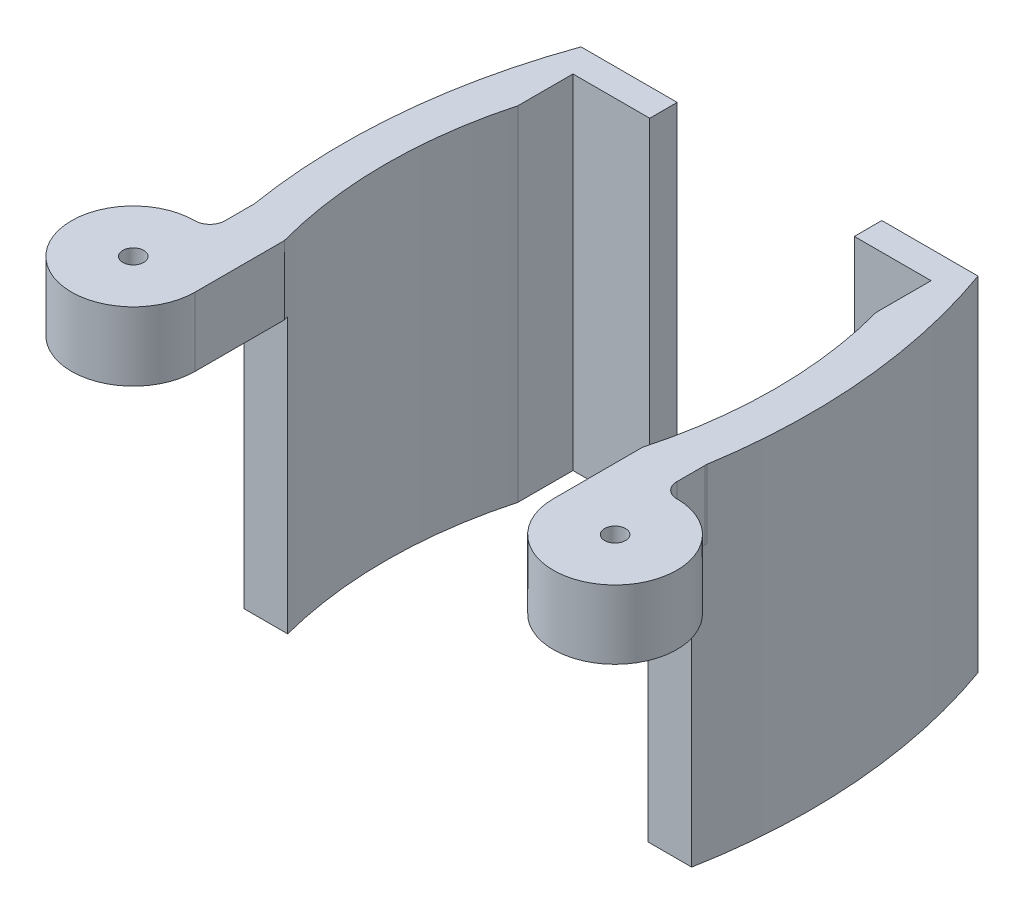
SolidWorks part; units mm, degrees
ref_plane "Front Plane" through (0, 0, 0) normal (0, 0, 1) x (1, 0, 0)
ref_plane "Top Plane" through (0, 0, 0) normal (0, 1, 0) x (1, 0, 0)
ref_plane "Right Plane" through (0, 0, 0) normal (1, 0, 0) x (0, 0, -1)
sketch "Sketch1" plane through (0, 0, 0) normal (0, 1, 0) x (1, 0, 0)
  line L0 (-9.8555, -63.7645) -> (-9.8555, -55.7645)
  line L1 (-9.8555, -21.7645) -> (-9.8555, -13.7645)
  line L2 (-9.8555, -13.7645) -> (-21.0253, -13.7645)
  line L3 (-21.0253, -13.7645) -> (-21.0253, -9.7645)
  line L4 (-21.0253, -9.7645) -> (-7.0253, -9.7645)
  line L5 (-35.9177, -13.7645) -> (-35.9177, -65.301) construction
  line L6 (-50.8101, -9.7645) -> (-64.8101, -9.7645)
  line L7 (-50.8101, -13.7645) -> (-50.8101, -9.7645)
  line L8 (-61.9799, -13.7645) -> (-50.8101, -13.7645)
  line L9 (-61.9799, -21.7645) -> (-61.9799, -13.7645)
  line L10 (-61.9799, -63.7645) -> (-61.9799, -55.7645)
  arc A0 (-9.8555, -63.7645) -> (-3.3512, -55.1175) centre (-0.8555, -63.7645) ccw
  arc A1 (-9.8555, -55.7645) -> (-9.8555, -21.7645) centre (-72.1785, -38.7645) ccw
  arc A2 (-7.0253, -9.7645) -> (-3.3512, -55.1175) centre (-89.1976, -39.2467) cw
  arc A3 (-64.8101, -9.7645) -> (-68.4842, -55.1175) centre (17.3623, -39.2467) ccw
  arc A4 (-61.9799, -55.7645) -> (-61.9799, -21.7645) centre (0.3432, -38.7645) cw
  arc A5 (-61.9799, -63.7645) -> (-68.4842, -55.1175) centre (-70.9799, -63.7645) cw
  dimension "D4" = 64.6
  dimension "D5" = 9
  dimension "D1" = 8
  dimension "D2" = 8
  dimension "D3" = 4
  dimension "D6" = 50
  dimension "D7" = 14
  dimension "D8" = 4.9
  dimension "D9" = 11.1698
extrude "Boss-Extrude1" add sketch "Sketch1" against normal blind 50
sketch "Sketch2" plane through (0, -50, 0) normal (0, -1, 0) x (1, 0, 0)
  circle A0 centre (-70.9799, 63.7645) radius 9
  circle A1 centre (-0.8555, 63.7645) radius 9
extrude "Cut-Extrude1" cut sketch "Sketch2" against normal blind 40
sketch "Sketch3" plane through (0, -50, 0) normal (0, -1, 0) x (1, 0, 0)
  line L0 (-68.4842, 55.1175) -> (-62.1528, 55.1175)
  line L1 (-62.1528, 55.1175) -> (-3.3512, 55.1175)
  line L2 (-3.3512, 55.1175) -> (-3.3512, 65.1021)
  line L3 (-3.3512, 65.1021) -> (-68.4842, 65.1021)
  line L4 (-68.4842, 65.1021) -> (-68.4842, 55.1175)
  arc A0 (-61.9799, 55.7645) -> (-61.9799, 21.7645) centre (0.3432, 38.7645) ccw construction
extrude "Cut-Extrude2" cut sketch "Sketch3" against normal blind 40
sketch "Sketch4" plane through (0, 0, 0) normal (0, 1, 0) x (1, 0, 0)
  line L0 (-68.8006, -53.2984) -> (-66.6672, -54.3894)
  line L1 (-66.6672, -54.3894) -> (-69.1301, -56.5741)
  line L2 (-69.1301, -56.5741) -> (-70.1938, -54.7989)
  line L3 (-3.0222, -53.2343) -> (-4.8299, -54.3174)
  line L4 (-4.8299, -54.3174) -> (-2.8281, -56.5741)
  line L5 (-2.8281, -56.5741) -> (-1.5175, -54.7889)
  arc A0 (-70.1938, -54.7989) -> (-68.8006, -53.2984) centre (-70.0805, -53.5071) ccw
  arc A1 (-68.4842, -55.1175) -> (-61.9799, -63.7645) centre (-70.9799, -63.7645) ccw construction
  arc A2 (-3.0222, -53.2343) -> (-1.5175, -54.7889) centre (-1.6211, -53.3837) ccw
  arc A3 (-9.8555, -63.7645) -> (-3.3512, -55.1175) centre (-0.8555, -63.7645) ccw construction
  arc A4 (-64.8101, -9.7645) -> (-68.4842, -55.1175) centre (17.3623, -39.2467) ccw construction
  arc A5 (-3.3512, -55.1175) -> (-7.0253, -9.7645) centre (-89.1976, -39.2467) ccw construction
extrude "Boss-Extrude2" add sketch "Sketch4" against normal blind 10
sketch "Sketch5" plane through (0, 0, 0) normal (0, 1, 0) x (1, 0, 0)
  circle A0 centre (-70.9799, -63.7645) radius 1.525
  circle A1 centre (-0.8555, -63.7645) radius 1.525
  dimension "D1" = 3.05
  dimension "D2" = 3.05
extrude "Cut-Extrude3" cut sketch "Sketch5" against normal blind 10
sketch "Sketch7" plane through (0, 0, 0) normal (0, 1, 0) x (1, 0, 0)
  line L0 (-9.8555, -63.7645) -> (-9.8555, -68.7645)
  line L1 (8.1445, -63.7645) -> (8.1445, -68.7645)
  line L2 (-61.9799, -63.7645) -> (-61.9799, -68.7645)
  line L3 (-79.9799, -63.7645) -> (-79.9799, -68.7645)
  circle A0 centre (-70.9799, -68.7645) radius 9
  circle A2 centre (-70.9799, -63.7645) radius 9
  circle A3 centre (-0.8555, -63.7645) radius 9
  circle A4 centre (-0.8555, -68.7645) radius 9
  arc M3 (-9.8555, -63.7645) -> (-1.5175, -54.7889) centre (-0.8555, -63.7645) ccw
  dimension "D3" = 18
  dimension "D4" = 18
  dimension "D1" = 5
  dimension "D2" = 5
extrude "Boss-Extrude3" add sketch "Sketch7" against normal up to surface (10 mm away) contours A4 A3 | A4 L1 M3 | A4 L0 M3 | A2 A0 L2 | A2 A0 | A2 L3 A0
sketch "Sketch8" plane through (0, 0, 0) normal (0, 1, 0) x (1, 0, 0)
  circle A0 centre (-70.9799, -63.7645) radius 1.525
  circle A1 centre (-0.8555, -63.7645) radius 1.525
extrude "Boss-Extrude4" add sketch "Sketch8" against normal up to surface (10 mm away) up to face at (-0.8555, -10, 65.2895)
sketch "Sketch9" plane through (0, 0, 0) normal (0, 1, 0) x (1, 0, 0)
  line L0 (-68.8006, -53.2984) -> (-68.8006, -60.0453)
  line L1 (-3.0246, -53.2357) -> (-3.0246, -60.0298)
  line L2 (-79.9799, -53.2984) -> (-79.9799, -68.7645)
  line L3 (-68.8006, -53.2984) -> (-79.9799, -53.2984)
  line L4 (8.1445, -68.7645) -> (8.1445, -53.2357)
  line L5 (8.1445, -53.2357) -> (-3.0246, -53.2357)
  circle A0 centre (-70.9698, -68.7687) radius 8.9891
  circle A1 centre (-0.8555, -68.7645) radius 9
  arc A2 (-70.9698, -59.7796) -> (-68.8006, -57.6104) centre (-70.9698, -57.6104) ccw
  arc A3 (-0.8555, -59.7645) -> (-3.0246, -57.5955) centre (-0.8555, -57.5955) cw
  arc A4 (-70.9698, -59.7796) -> (-79.9799, -68.7645) centre (-70.9949, -68.7645) ccw
  line M5 (8.1445, -68.7645) -> (8.1445, -63.7645)
  arc M6 (8.1445, -63.7645) -> (-1.5175, -54.7889) centre (-0.8555, -63.7645) ccw
  arc M7 (-1.5175, -54.7889) -> (-3.0222, -53.2343) centre (-1.6211, -53.3837) cw
  dimension "D1" = 2.1692
  dimension "D2" = 90
  dimension "D3" = 12.7244
extrude "Cut-Extrude5" cut sketch "Sketch9" against normal blind 10 contours A4 A2 L0 L3 L2 | A3 A1 L1 M5 M6 M7 | L4 L5 L1 M7 M6
sketch "Sketch10" plane through (0, 0, 0) normal (0, 1, 0) x (1, 0, 0)
  circle A2 centre (-70.9799, -68.7645) radius 1.525
  circle A3 centre (-0.8555, -68.7645) radius 1.525
  dimension "D1" = 3.05
  dimension "D2" = 3.05
extrude "Cut-Extrude6" cut sketch "Sketch10" against normal blind 10
